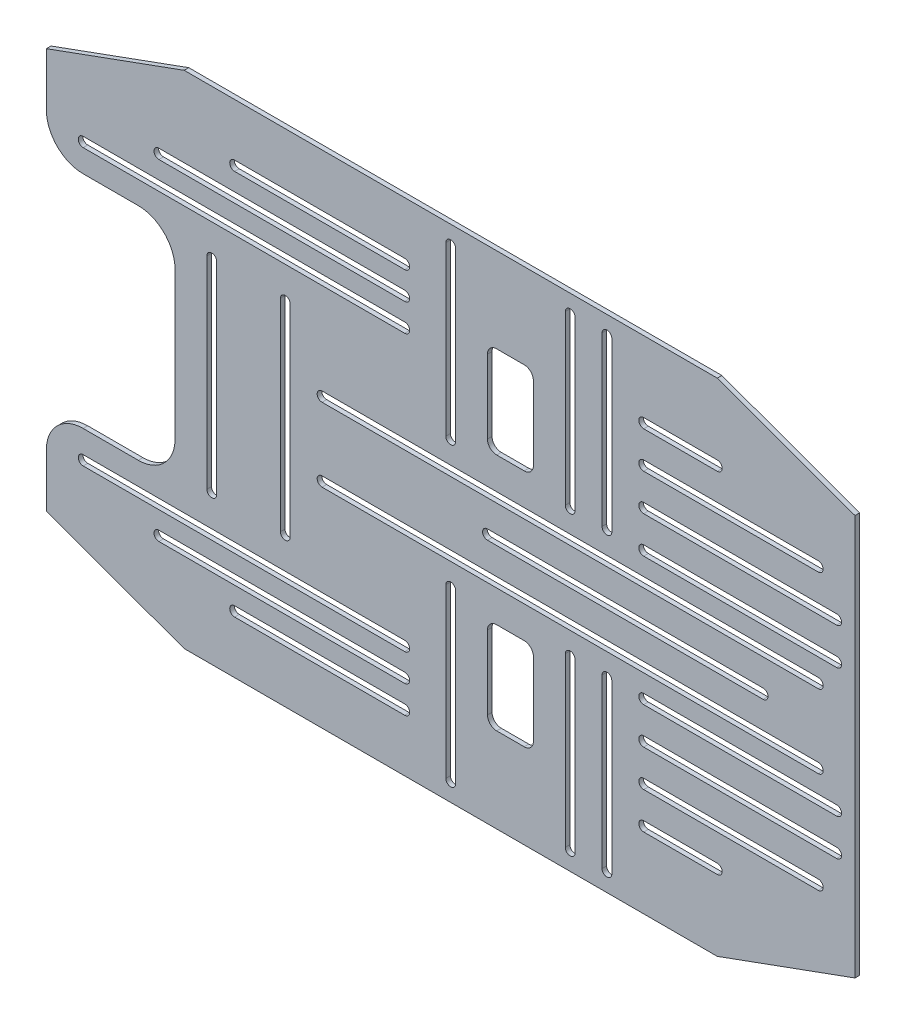
SolidWorks part; units mm, degrees
material "6061-T6 (SS)"
ref_plane "Front Plane" through (0, 0, 0) normal (0, 0, 1) x (1, 0, 0)
ref_plane "Top Plane" through (0, 0, 0) normal (0, 1, 0) x (1, 0, 0)
ref_plane "Right Plane" through (0, 0, 0) normal (1, 0, 0) x (0, 0, -1)
sketch "Sketch1" plane through (0, 0, 0) normal (0, 0, 1) x (1, 0, 0)
  line L0 (-279.4, 138.3894) -> (-184.2141, 173.0342)
  line L2 (-184.2141, 173.0342) -> (184.2141, 173.0342)
  line L3 (-254, 147.6342) -> (254, 147.6342) construction
  line L4 (184.2141, 173.0342) -> (279.4, 138.3894)
  line L5 (279.4, 138.3894) -> (279.4, -138.3894)
  line L10 (-254, 147.6342) -> (-254, -147.6342) construction
  line L11 (279.4, -138.3894) -> (184.2141, -173.0342)
  line L12 (184.2141, -173.0342) -> (-184.2141, -173.0342)
  line L13 (-254, -147.6342) -> (254, -147.6342) construction
  line L14 (-184.2141, -173.0342) -> (-279.4, -138.3894)
  line L16 (-279.4, -76.2) -> (-190.5, -76.2)
  line L17 (-190.5, -76.2) -> (-190.5, 76.2)
  line L18 (-190.5, 76.2) -> (-279.4, 76.2)
  line L19 (-279.4, 76.2) -> (-279.4, 138.3894)
  line L20 (254, 147.6342) -> (254, -147.6342) construction
  line L24 (-279.4, -138.3894) -> (-279.4, -76.2)
  point P6 (0, 147.6342)
  point P7 (-254, 0)
  point P13 (-190.5, 0)
  dimension "D1" = 508
  dimension "D2" = 295.2684
  dimension "D3" = 20
  dimension "D4" = 20
  dimension "D5" = 20
  dimension "D6" = 20
  dimension "D7" = 25.4
  dimension "D8" = 25.4
  dimension "D9" = 25.4
  dimension "D10" = 152.4
  dimension "D11" = 88.9
extrude "Boss-Extrude1" add sketch "Sketch1" along normal blind 3.175
fillet "Fillet3" radius 25.4 4 edges at (-279.4, 76.2, 1.5875) (-190.5, 76.2, 1.5875) (-190.5, -76.2, 1.5875) (-279.4, -76.2, 1.5875)
sketch "Sketch4" plane through (0, 0, 3.175) normal (0, 0, 1) x (1, 0, 0)
  line L0 (-254, 95.25) -> (-31.75, 95.25) construction
  line L1 (-254, 98.6282) -> (-31.75, 98.6282)
  line L2 (-254, 91.8718) -> (-31.75, 91.8718)
  line L3 (-201.6606, 114.3) -> (-31.75, 114.3) construction
  line L4 (-201.6606, 117.6782) -> (-31.75, 117.6782)
  line L5 (-201.6606, 110.9218) -> (-31.75, 110.9218)
  line L6 (-149.3211, 133.35) -> (-31.75, 133.35) construction
  line L7 (-149.3211, 136.7282) -> (-31.75, 136.7282)
  line L8 (-149.3211, 129.9718) -> (-31.75, 129.9718)
  line L9 (-165.1, 69.85) -> (-165.1, -69.85) construction
  line L10 (-161.7218, 69.85) -> (-161.7218, -69.85)
  line L11 (-168.4782, 69.85) -> (-168.4782, -69.85)
  line L12 (-114.3, 69.85) -> (-114.3, -69.85) construction
  line L13 (-110.9218, 69.85) -> (-110.9218, -69.85)
  line L14 (-117.6782, 69.85) -> (-117.6782, -69.85)
  line L15 (-254, 76.2) -> (-215.9, 76.2) construction
  line L16 (254, 95.25) -> (184.2141, 120.65) construction
  line L17 (-254, 95.25) -> (-149.3211, 133.35) construction
  line L18 (-184.2141, 173.0342) -> (-279.4, 138.3894) construction
  line L19 (279.4, 0) -> (-279.4, 0) construction
  line L20 (279.4, -138.3894) -> (279.4, 138.3894) construction
  line L21 (0, -12.6623) -> (0, 49987.3377) construction
  line L22 (-279.4, 138.3894) -> (-279.4, 101.6) construction
  line L23 (0, 160.3342) -> (0, 44.45) construction
  line L24 (31.75, 114.3) -> (50.8, 114.3)
  line L25 (25.4, 107.95) -> (25.4, 57.15)
  line L26 (31.75, 50.8) -> (50.8, 50.8)
  line L27 (57.15, 107.95) -> (57.15, 57.15)
  line L28 (3.3782, 160.3342) -> (3.3782, 44.45)
  line L29 (-3.3782, 160.3342) -> (-3.3782, 44.45)
  line L30 (-88.9, 25.4) -> (254, 25.4) construction
  line L31 (-88.9, 28.7782) -> (254, 28.7782)
  line L32 (-88.9, 22.0218) -> (254, 22.0218)
  line L33 (82.55, 44.45) -> (82.55, 160.3342) construction
  line L34 (79.1718, 44.45) -> (79.1718, 160.3342)
  line L35 (85.9282, 44.45) -> (85.9282, 160.3342)
  line L36 (107.95, 160.3342) -> (107.95, 44.45) construction
  line L37 (111.3282, 160.3342) -> (111.3282, 44.45)
  line L38 (104.5718, 160.3342) -> (104.5718, 44.45)
  line L39 (133.35, 120.65) -> (184.2141, 120.65) construction
  line L40 (133.35, 124.0282) -> (184.2141, 124.0282)
  line L41 (133.35, 117.2718) -> (184.2141, 117.2718)
  line L42 (133.35, 95.25) -> (254, 95.25) construction
  line L43 (133.35, 98.6282) -> (254, 98.6282)
  line L44 (133.35, 91.8718) -> (254, 91.8718)
  line L45 (133.35, 69.85) -> (266.7, 69.85) construction
  line L46 (133.35, 73.2282) -> (266.7, 73.2282)
  line L47 (133.35, 66.4718) -> (266.7, 66.4718)
  line L48 (133.35, 44.45) -> (266.7, 44.45) construction
  line L49 (133.35, 47.8282) -> (266.7, 47.8282)
  line L50 (133.35, 41.0718) -> (266.7, 41.0718)
  line L51 (279.4, 138.3894) -> (184.2141, 173.0342) construction
  line L52 (184.2141, 173.0342) -> (-184.2141, 173.0342) construction
  line L53 (-190.5, 50.8) -> (-190.5, -50.8) construction
  line L54 (-254, -95.25) -> (-31.75, -95.25) construction
  line L55 (-254, -98.6282) -> (-31.75, -98.6282)
  line L56 (-254, -91.8718) -> (-31.75, -91.8718)
  line L57 (-201.6606, -114.3) -> (-31.75, -114.3) construction
  line L58 (-201.6606, -117.6782) -> (-31.75, -117.6782)
  line L59 (-201.6606, -110.9218) -> (-31.75, -110.9218)
  line L60 (-149.3211, -133.35) -> (-31.75, -133.35) construction
  line L61 (-149.3211, -136.7282) -> (-31.75, -136.7282)
  line L62 (-149.3211, -129.9718) -> (-31.75, -129.9718)
  line L63 (0, -160.3342) -> (0, -44.45) construction
  line L64 (3.3782, -160.3342) -> (3.3782, -44.45)
  line L65 (-3.3782, -160.3342) -> (-3.3782, -44.45)
  line L66 (-88.9, -25.4) -> (254, -25.4) construction
  line L67 (-88.9, -28.7782) -> (254, -28.7782)
  line L68 (-88.9, -22.0218) -> (254, -22.0218)
  line L69 (82.55, -44.45) -> (82.55, -160.3342) construction
  line L70 (79.1718, -44.45) -> (79.1718, -160.3342)
  line L71 (85.9282, -44.45) -> (85.9282, -160.3342)
  line L72 (107.95, -160.3342) -> (107.95, -44.45) construction
  line L73 (111.3282, -160.3342) -> (111.3282, -44.45)
  line L74 (104.5718, -160.3342) -> (104.5718, -44.45)
  line L75 (133.35, -120.65) -> (184.2141, -120.65) construction
  line L76 (133.35, -124.0282) -> (184.2141, -124.0282)
  line L77 (133.35, -117.2718) -> (184.2141, -117.2718)
  line L78 (133.35, -95.25) -> (254, -95.25) construction
  line L79 (133.35, -98.6282) -> (254, -98.6282)
  line L80 (133.35, -91.8718) -> (254, -91.8718)
  line L81 (133.35, -69.85) -> (266.7, -69.85) construction
  line L82 (133.35, -73.2282) -> (266.7, -73.2282)
  line L83 (133.35, -66.4718) -> (266.7, -66.4718)
  line L84 (133.35, -44.45) -> (266.7, -44.45) construction
  line L85 (133.35, -47.8282) -> (266.7, -47.8282)
  line L86 (133.35, -41.0718) -> (266.7, -41.0718)
  line L87 (57.15, -107.95) -> (57.15, -57.15)
  line L88 (31.75, -50.8) -> (50.8, -50.8)
  line L89 (25.4, -107.95) -> (25.4, -57.15)
  line L90 (31.75, -114.3) -> (50.8, -114.3)
  line L91 (25.4, 0) -> (215.9, 0) construction
  line L92 (25.4, 3.3782) -> (215.9, 3.3782)
  line L93 (25.4, -3.3782) -> (215.9, -3.3782)
  arc A0 (-254, 98.6282) -> (-254, 91.8718) centre (-254, 95.25) ccw
  arc A1 (-31.75, 91.8718) -> (-31.75, 98.6282) centre (-31.75, 95.25) ccw
  arc A2 (-201.6606, 117.6782) -> (-201.6606, 110.9218) centre (-201.6606, 114.3) ccw
  arc A3 (-31.75, 110.9218) -> (-31.75, 117.6782) centre (-31.75, 114.3) ccw
  arc A4 (-149.3211, 136.7282) -> (-149.3211, 129.9718) centre (-149.3211, 133.35) ccw
  arc A5 (-31.75, 129.9718) -> (-31.75, 136.7282) centre (-31.75, 133.35) ccw
  arc A6 (-161.7218, 69.85) -> (-168.4782, 69.85) centre (-165.1, 69.85) ccw
  arc A7 (-168.4782, -69.85) -> (-161.7218, -69.85) centre (-165.1, -69.85) ccw
  arc A8 (-110.9218, 69.85) -> (-117.6782, 69.85) centre (-114.3, 69.85) ccw
  arc A9 (-117.6782, -69.85) -> (-110.9218, -69.85) centre (-114.3, -69.85) ccw
  arc A10 (-254, -98.6282) -> (-254, -91.8718) centre (-254, -95.25) cw
  arc A11 (-31.75, -91.8718) -> (-31.75, -98.6282) centre (-31.75, -95.25) cw
  arc A12 (3.3782, 160.3342) -> (-3.3782, 160.3342) centre (0, 160.3342) ccw
  arc A13 (-3.3782, 44.45) -> (3.3782, 44.45) centre (0, 44.45) ccw
  arc A14 (-88.9, 28.7782) -> (-88.9, 22.0218) centre (-88.9, 25.4) ccw
  arc A15 (254, 22.0218) -> (254, 28.7782) centre (254, 25.4) ccw
  arc A16 (79.1718, 44.45) -> (85.9282, 44.45) centre (82.55, 44.45) ccw
  arc A17 (85.9282, 160.3342) -> (79.1718, 160.3342) centre (82.55, 160.3342) ccw
  arc A18 (111.3282, 160.3342) -> (104.5718, 160.3342) centre (107.95, 160.3342) ccw
  arc A19 (104.5718, 44.45) -> (111.3282, 44.45) centre (107.95, 44.45) ccw
  arc A20 (133.35, 124.0282) -> (133.35, 117.2718) centre (133.35, 120.65) ccw
  arc A21 (184.2141, 117.2718) -> (184.2141, 124.0282) centre (184.2141, 120.65) ccw
  arc A22 (133.35, 98.6282) -> (133.35, 91.8718) centre (133.35, 95.25) ccw
  arc A23 (254, 91.8718) -> (254, 98.6282) centre (254, 95.25) ccw
  arc A24 (133.35, 73.2282) -> (133.35, 66.4718) centre (133.35, 69.85) ccw
  arc A25 (266.7, 66.4718) -> (266.7, 73.2282) centre (266.7, 69.85) ccw
  arc A26 (133.35, 47.8282) -> (133.35, 41.0718) centre (133.35, 44.45) ccw
  arc A27 (266.7, 41.0718) -> (266.7, 47.8282) centre (266.7, 44.45) ccw
  arc A28 (-201.6606, -117.6782) -> (-201.6606, -110.9218) centre (-201.6606, -114.3) cw
  arc A29 (-31.75, -110.9218) -> (-31.75, -117.6782) centre (-31.75, -114.3) cw
  arc A30 (-149.3211, -136.7282) -> (-149.3211, -129.9718) centre (-149.3211, -133.35) cw
  arc A31 (-31.75, -129.9718) -> (-31.75, -136.7282) centre (-31.75, -133.35) cw
  arc A32 (3.3782, -160.3342) -> (-3.3782, -160.3342) centre (0, -160.3342) cw
  arc A33 (-3.3782, -44.45) -> (3.3782, -44.45) centre (0, -44.45) cw
  arc A34 (-88.9, -28.7782) -> (-88.9, -22.0218) centre (-88.9, -25.4) cw
  arc A35 (254, -22.0218) -> (254, -28.7782) centre (254, -25.4) cw
  arc A36 (79.1718, -44.45) -> (85.9282, -44.45) centre (82.55, -44.45) cw
  arc A37 (85.9282, -160.3342) -> (79.1718, -160.3342) centre (82.55, -160.3342) cw
  arc A38 (111.3282, -160.3342) -> (104.5718, -160.3342) centre (107.95, -160.3342) cw
  arc A39 (104.5718, -44.45) -> (111.3282, -44.45) centre (107.95, -44.45) cw
  arc A40 (133.35, -124.0282) -> (133.35, -117.2718) centre (133.35, -120.65) cw
  arc A41 (184.2141, -117.2718) -> (184.2141, -124.0282) centre (184.2141, -120.65) cw
  arc A42 (133.35, -98.6282) -> (133.35, -91.8718) centre (133.35, -95.25) cw
  arc A43 (254, -91.8718) -> (254, -98.6282) centre (254, -95.25) cw
  arc A44 (133.35, -73.2282) -> (133.35, -66.4718) centre (133.35, -69.85) cw
  arc A45 (266.7, -66.4718) -> (266.7, -73.2282) centre (266.7, -69.85) cw
  arc A46 (133.35, -47.8282) -> (133.35, -41.0718) centre (133.35, -44.45) cw
  arc A47 (266.7, -41.0718) -> (266.7, -47.8282) centre (266.7, -44.45) cw
  arc A48 (25.4, 3.3782) -> (25.4, -3.3782) centre (25.4, 0) ccw
  arc A49 (215.9, -3.3782) -> (215.9, 3.3782) centre (215.9, 0) ccw
  arc A50 (25.4, -107.95) -> (31.75, -114.3) centre (31.75, -107.95) ccw
  arc A51 (31.75, -50.8) -> (25.4, -57.15) centre (31.75, -57.15) ccw
  arc A52 (57.15, -57.15) -> (50.8, -50.8) centre (50.8, -57.15) ccw
  arc A53 (57.15, -107.95) -> (50.8, -114.3) centre (50.8, -107.95) cw
  arc A54 (50.8, 50.8) -> (57.15, 57.15) centre (50.8, 57.15) ccw
  arc A55 (25.4, 57.15) -> (31.75, 50.8) centre (31.75, 57.15) ccw
  arc A56 (50.8, 114.3) -> (57.15, 107.95) centre (50.8, 107.95) cw
  arc A57 (31.75, 114.3) -> (25.4, 107.95) centre (31.75, 107.95) ccw
  point P2 (-142.875, 95.25)
  point P7 (-116.7053, 114.3)
  point P14 (-90.5356, 133.35)
  point P21 (-165.1, 0)
  point P28 (-114.3, 0)
  point P43 (0, 0)
  point P53 (0, 102.3921)
  point P62 (82.55, 25.4)
  point P69 (82.55, 102.3921)
  point P76 (107.95, 102.3921)
  point P83 (158.782, 120.65)
  point P90 (193.675, 95.25)
  point P97 (200.025, 69.85)
  point P104 (200.025, 44.45)
  point P115 (120.65, 0)
  point P125 (25.4, -114.3)
  point P131 (25.4, -50.8)
  point P136 (-142.875, -95.25)
  point P143 (-116.7053, -114.3)
  point P150 (-90.5356, -133.35)
  point P157 (0, -102.3921)
  point P164 (82.55, -25.4)
  point P171 (82.55, -102.3921)
  point P178 (107.95, -102.3921)
  point P185 (158.782, -120.65)
  point P192 (193.675, -95.25)
  point P199 (200.025, -69.85)
  point P206 (200.025, -44.45)
  point P214 (57.15, -50.8)
  point P219 (57.15, -114.3)
  point P222 (57.15, 50.8)
  point P225 (25.4, 50.8)
  point P228 (57.15, 114.3)
  point P231 (25.4, 114.3)
  dimension "D1" = 6.7564
  dimension "D23" = 6.35
  dimension "D2" = 19.05
  dimension "D3" = 19.05
  dimension "D4" = 19.05
  dimension "D5" = 50.8
  dimension "D6" = 31.75
  dimension "D7" = 31.75
  dimension "D8" = 63.5
  dimension "D9" = 25.4
  dimension "D10" = 25.4
  dimension "D11" = 25.4
  dimension "D12" = 25.4
  dimension "D13" = 25.4
  dimension "D14" = 25.4
  dimension "D15" = 25.4
  dimension "D16" = 12.7
  dimension "D17" = 12.7
  dimension "D18" = 25.4
  dimension "D19" = 25.4
  dimension "D20" = 25.4
  dimension "D21" = 25.4
  dimension "D22" = 63.5
extrude "Cut-Extrude3" cut sketch "Sketch4" against normal through all
ref_plane "MidPlane" through (0, 0, 1.5875) normal (0, 0, 1) x (1, 0, 0)
scale "Scale1" scale about centroid uniform scaling yes scale factor 0.35
